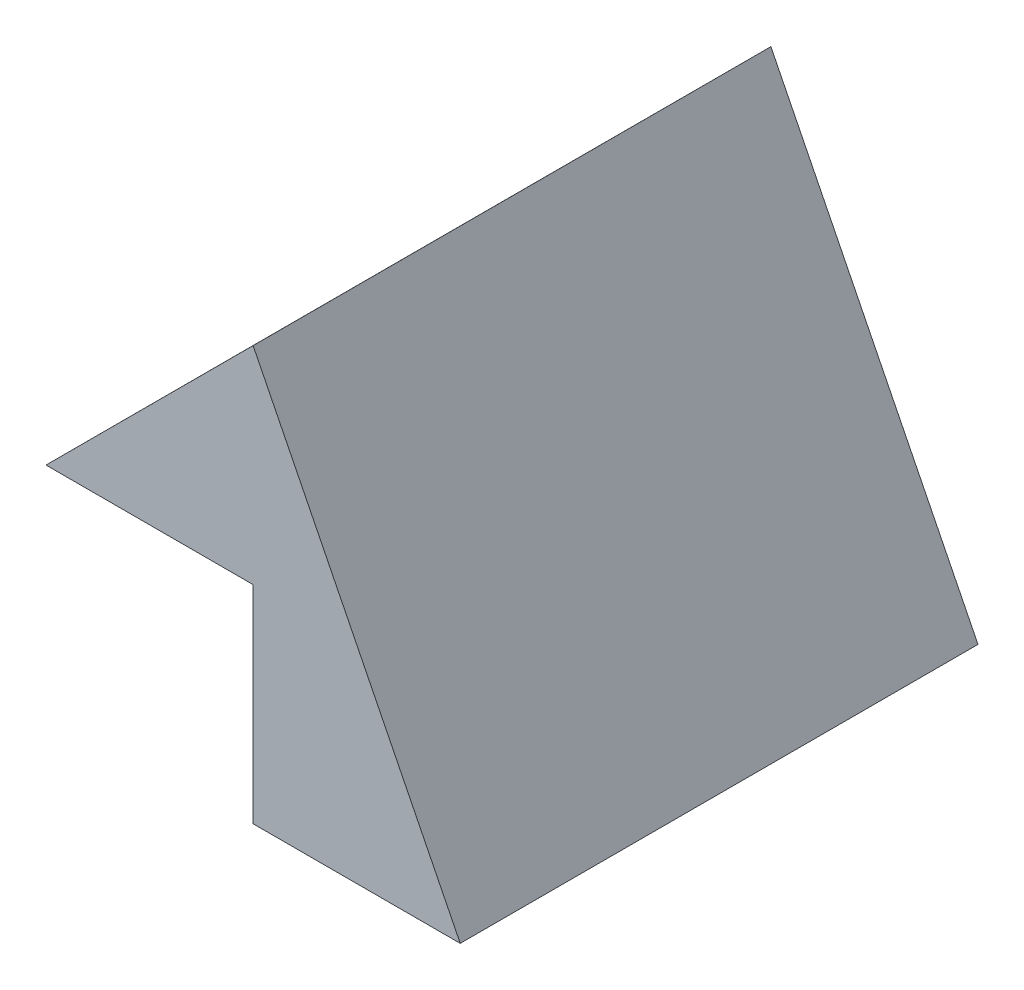
SolidWorks part; units mm, degrees
ref_plane "Front Plane" through (0, 0, 0) normal (0, 0, 1) x (1, 0, 0)
ref_plane "Top Plane" through (0, 0, 0) normal (0, 1, 0) x (1, 0, 0)
ref_plane "Right Plane" through (0, 0, 0) normal (1, 0, 0) x (0, 0, -1)
sketch "Sketch1" plane through (0, 0, 0) normal (0, 0, 1) x (1, 0, 0)
  line L0 (-20, 10) -> (-10, 19.9961)
  line L1 (-10, 19.9961) -> (0, 0)
  line L2 (0, 0) -> (-10, 0)
  line L3 (-10, 0) -> (-10, 10)
  line L4 (-10, 10) -> (-20, 10)
  dimension "D1" = 10
  dimension "D2" = 10
  dimension "D3" = 10
  dimension "D4" = 19.9961
  dimension "D5" = 10
extrude "Boss-Extrude1" add sketch "Sketch1" along normal blind 25
